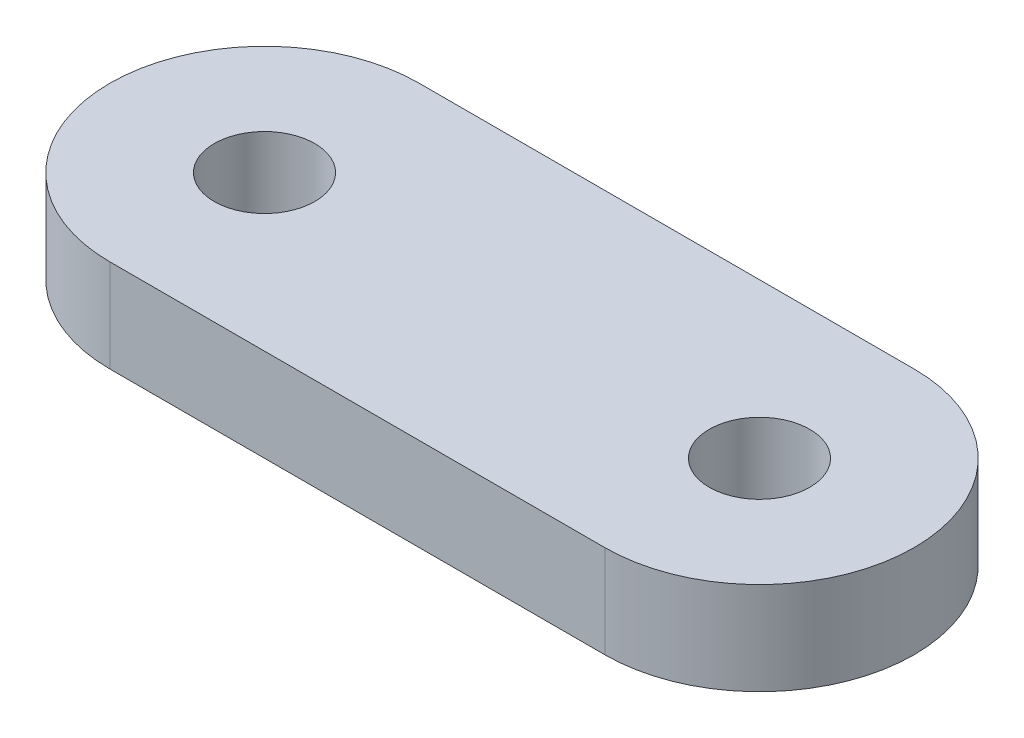
SolidWorks part; units mm, degrees
ref_plane "Front Plane" through (0, 0, 0) normal (0, 0, 1) x (1, 0, 0)
ref_plane "Top Plane" through (0, 0, 0) normal (0, 1, 0) x (1, 0, 0)
ref_plane "Right Plane" through (0, 0, 0) normal (1, 0, 0) x (0, 0, -1)
sketch "Sketch1" plane through (0, 0, 0) normal (0, 1, 0) x (1, 0, 0)
  line L0 (0, 0) -> (16, 0) construction
  line L1 (0, 5) -> (16, 5)
  line L2 (0, -5) -> (16, -5)
  arc A0 (0, 5) -> (0, -5) centre (0, 0) ccw
  arc A1 (16, -5) -> (16, 5) centre (16, 0) ccw
  circle A2 centre (0, 0) radius 1.625
  circle A3 centre (16, 0) radius 1.625
  point P3 (8, 0)
  dimension "D2" = 5
  dimension "D3" = 3.25
  dimension "D1" = 16
extrude "Boss-Extrude1" add sketch "Sketch1" along normal blind 3
